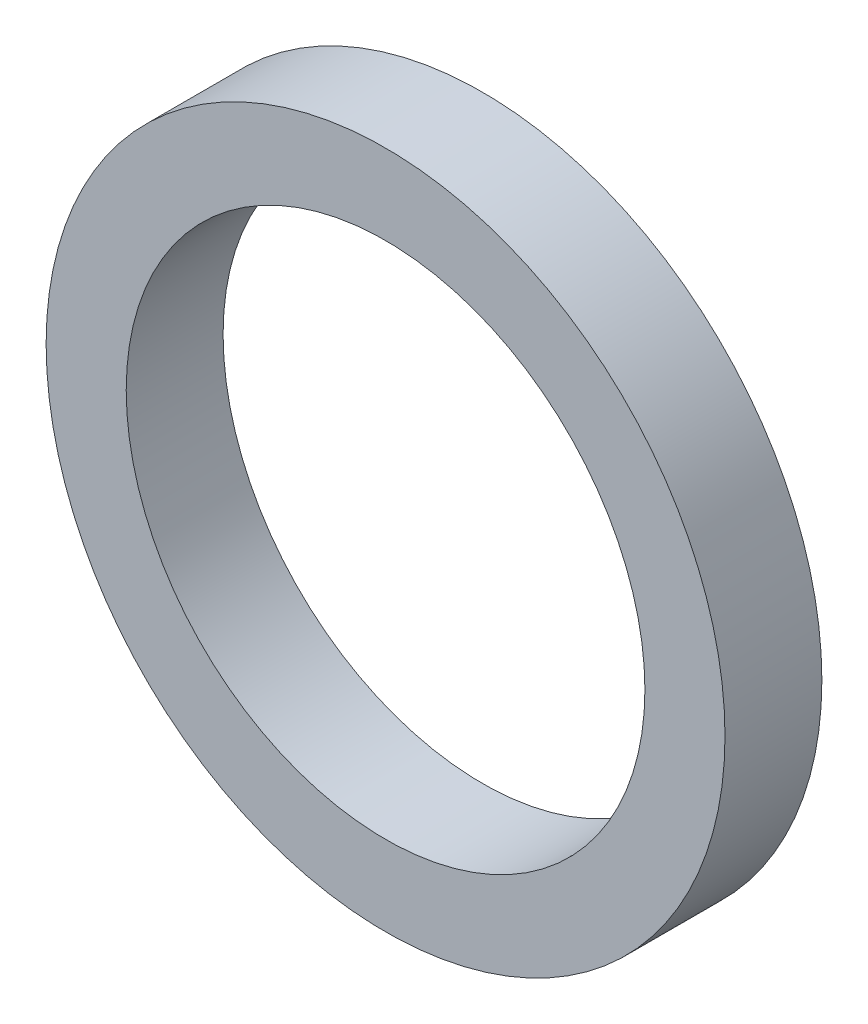
SolidWorks part; units mm, degrees
material "Cromium"
ref_plane "Front" through (0, 0, 0) normal (0, 0, 1) x (1, 0, 0)
ref_plane "Top" through (0, 0, 0) normal (0, 1, 0) x (1, 0, 0)
ref_plane "Right" through (0, 0, 0) normal (1, 0, 0) x (0, 0, -1)
sketch "Sketch1" plane through (0, 0, 0) normal (0, 0, 1) x (1, 0, 0)
  circle A0 centre (0, 0) radius 133.5
  circle A1 centre (0, 0) radius 102
extrude "Boss-Extrude1" add sketch "Sketch1" along normal blind 38.1
